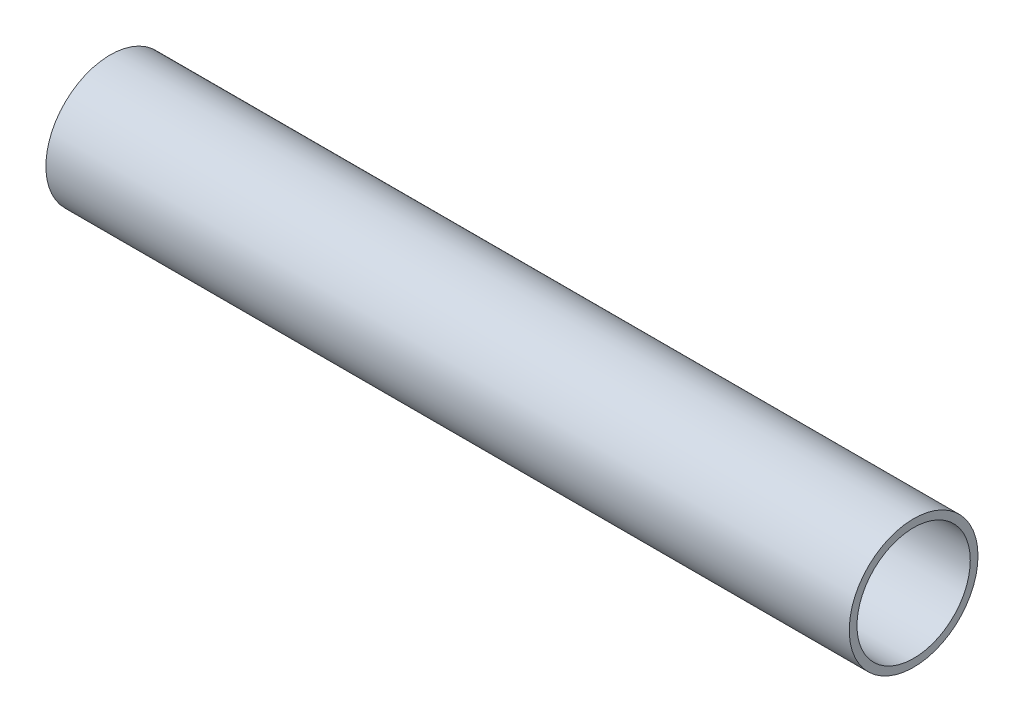
SolidWorks part; units mm, degrees
ref_plane "Plan de face" through (0, 0, 0) normal (0, 0, 1) x (1, 0, 0)
ref_plane "Plan de dessus" through (0, 0, 0) normal (0, 1, 0) x (1, 0, 0)
ref_plane "Plan de droite" through (0, 0, 0) normal (1, 0, 0) x (0, 0, -1)
sketch "Esquisse1" plane through (0, 0, 0) normal (1, 0, 0) x (0, 0, -1)
  circle A0 centre (0, 0) radius 12.5
  circle A1 centre (0, 0) radius 11
extrude "Boss.-Extru.1" add sketch "Esquisse1" along normal blind 156
